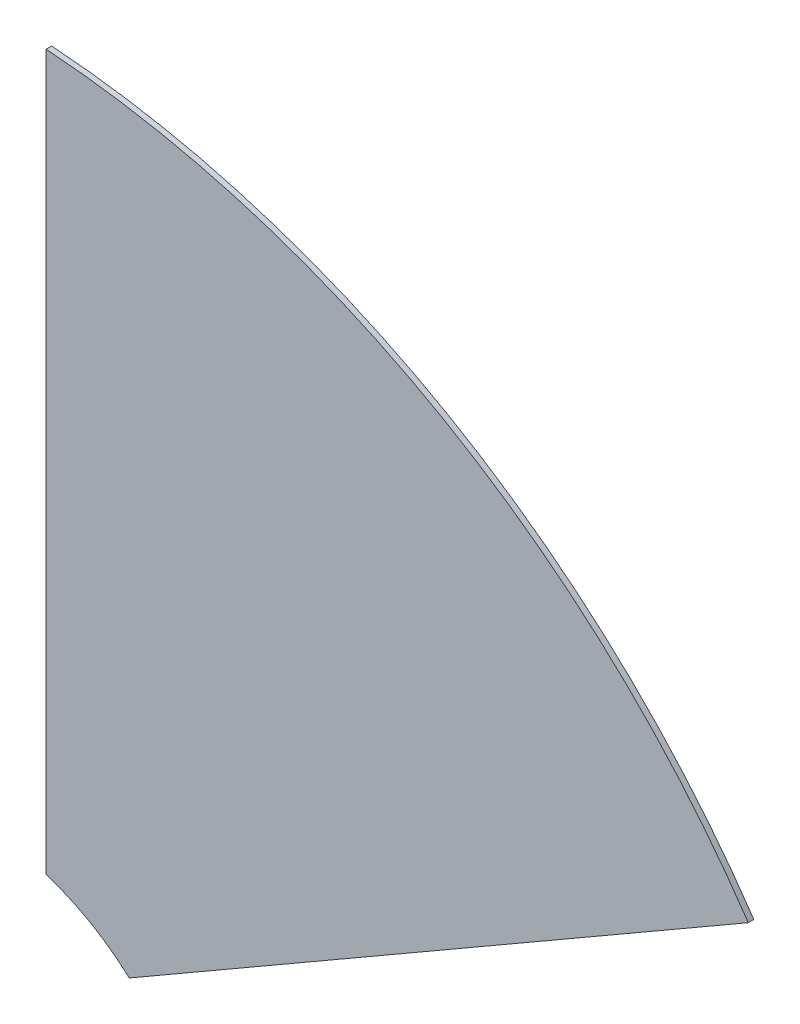
SolidWorks part; units mm, degrees
ref_plane "Front Plane" through (0, 0, 0) normal (0, 0, 1) x (1, 0, 0)
ref_plane "Top Plane" through (0, 0, 0) normal (0, 1, 0) x (1, 0, 0)
ref_plane "Right Plane" through (0, 0, 0) normal (1, 0, 0) x (0, 0, -1)
sketch "Sketch1" plane through (0, 0, 0) normal (0, 0, 1) x (1, 0, 0)
  line L0 (0, 0) -> (0, 266.7) construction
  line L1 (0, 0) -> (230.969, 133.35) construction
  line L2 (-25.4, 133.35) -> (25.4, 133.35)
  line L3 (128.1845, 44.678) -> (102.7845, 88.672)
  line L4 (-25.4, 133.35) -> (-25.4, 58.1987) construction
  line L5 (-25.4, 133.35) -> (-25.4, 265.4877) construction
  line L6 (25.4, 133.35) -> (25.4, 265.4877) construction
  line L7 (25.4, 133.35) -> (25.4, 58.1987) construction
  line L8 (102.7845, 88.672) -> (37.7016, 51.0964) construction
  line L9 (102.7845, 88.672) -> (217.2191, 154.7409) construction
  line L10 (128.1845, 44.678) -> (63.1016, 7.1023) construction
  line L11 (128.1845, 44.678) -> (242.6191, 110.7468) construction
  line L12 (25.4, 133.35) -> (19.05, 133.35)
  line L13 (102.7845, 88.672) -> (105.9595, 83.1728)
  line L14 (19.05, 133.35) -> (19.05, 60.5751) construction
  line L15 (19.05, 133.35) -> (19.05, 266.0188) construction
  line L16 (105.9595, 83.1728) -> (42.9346, 46.7854) construction
  line L17 (105.9595, 83.1728) -> (220.854, 149.5072) construction
  circle A0 centre (0, 0) radius 254
  circle A1 centre (0, 0) radius 76.2
  circle A2 centre (0, 0) radius 63.5 construction
  circle A3 centre (0, 0) radius 266.7 construction
  point P9 (0, 133.35)
  point P12 (115.4845, 66.675)
  dimension "D1" = 60
  dimension "D5" = 508
  dimension "D6" = 152.4
  dimension "D7" = 127
  dimension "D8" = 533.4
  dimension "D2" = 50.8
  dimension "D3" = 6.35
  dimension "D4" = 6.35
sketch "Sketch2" plane through (0, 0, 0) normal (0, 0, 1) x (1, 0, 0)
  line L0 (19.05, 266.0188) -> (19.05, 60.5751)
  line L1 (220.854, 149.5072) -> (42.9346, 46.7854)
  arc A0 (19.05, 266.0188) -> (220.854, 149.5072) centre (0, 0) cw
  arc A1 (19.05, 60.5751) -> (42.9346, 46.7854) centre (0, 0) cw
extrude "Boss-Extrude1" add sketch "Sketch2" along normal blind 1.5875
